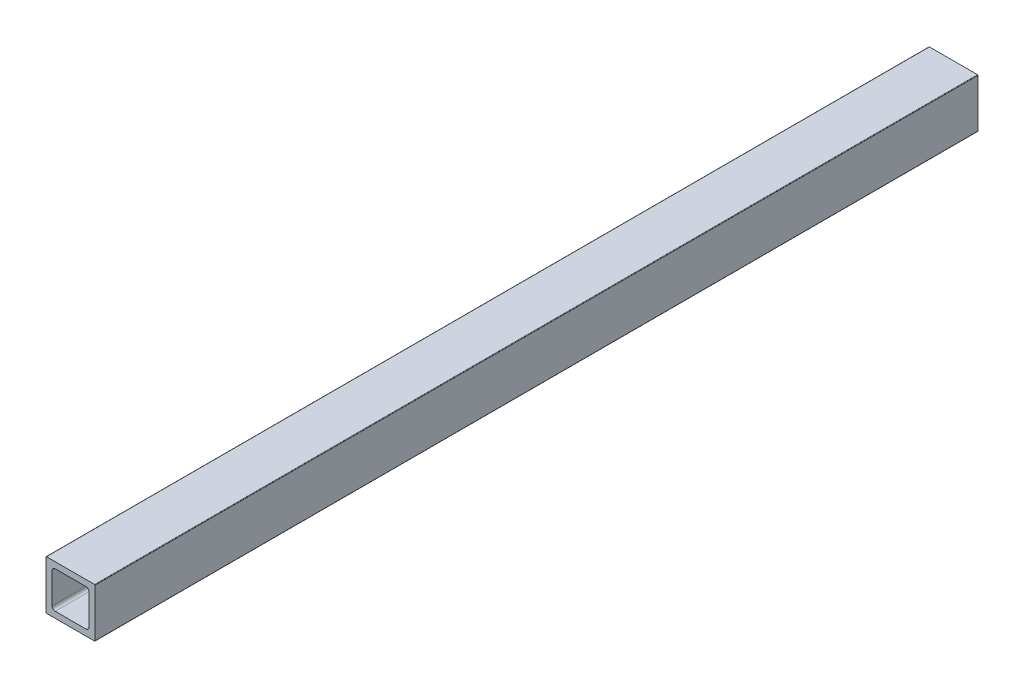
SolidWorks part; units mm, degrees
ref_plane "Front Plane" through (0, 0, 0) normal (0, 0, 1) x (1, 0, 0)
ref_plane "Top Plane" through (0, 0, 0) normal (0, 1, 0) x (1, 0, 0)
ref_plane "Right Plane" through (0, 0, 0) normal (1, 0, 0) x (0, 0, -1)
ref_plane "Plane1" through (0, 0, 0) normal (0, 0, -1) x (-1, 0, 0)
sketch "Sketch1" plane through (0, 0, 0) normal (0, 0, -1) x (-1, 0, 0)
  line L0 (-3.175, 20.6375) -> (-3.175, 4.7625)
  line L1 (-4.7625, 3.175) -> (-20.6375, 3.175)
  line L2 (-22.225, 4.7625) -> (-22.225, 20.6375)
  line L3 (-20.6375, 22.225) -> (-4.7625, 22.225)
  line L4 (0, 0.254) -> (0, 25.146)
  line L5 (-0.254, 25.4) -> (-25.146, 25.4)
  line L6 (-25.4, 25.146) -> (-25.4, 0.254)
  line L7 (-25.146, 0) -> (-0.254, 0)
  arc A0 (-3.175, 4.7625) -> (-4.7625, 3.175) centre (-4.7625, 4.7625) cw
  arc A1 (-20.6375, 3.175) -> (-22.225, 4.7625) centre (-20.6375, 4.7625) cw
  arc A2 (-22.225, 20.6375) -> (-20.6375, 22.225) centre (-20.6375, 20.6375) cw
  arc A3 (-4.7625, 22.225) -> (-3.175, 20.6375) centre (-4.7625, 20.6375) cw
  arc A4 (-0.254, 0) -> (0, 0.254) centre (-0.254, 0.254) ccw
  arc A5 (0, 25.146) -> (-0.254, 25.4) centre (-0.254, 25.146) ccw
  arc A6 (-25.146, 25.4) -> (-25.4, 25.146) centre (-25.146, 25.146) ccw
  arc A7 (-25.4, 0.254) -> (-25.146, 0) centre (-25.146, 0.254) ccw
  dimension "D1" = 25.4
  dimension "D2" = 25.4
  dimension "D3" = 19.05
  dimension "D4" = 3.175
  dimension "D5" = 19.05
extrude "Boss-Extrude1" add sketch "Sketch1" against normal blind 457.2
